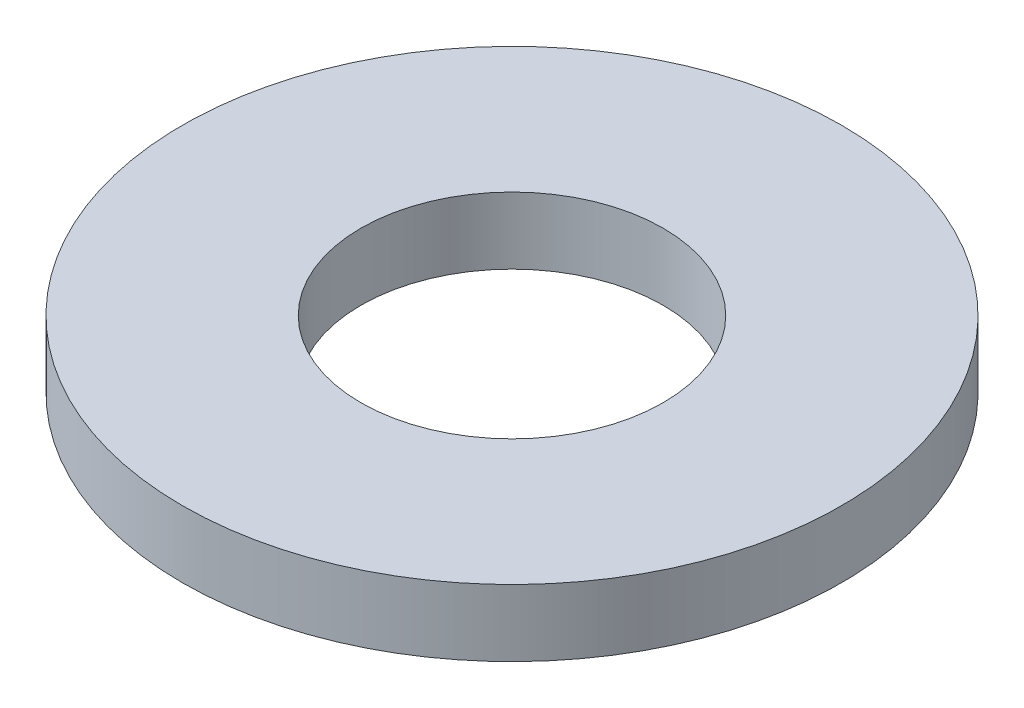
SolidWorks part; units mm, degrees
material "AISI 304"
ref_plane "Front Plane" through (0, 0, 0) normal (0, 0, 1) x (1, 0, 0)
ref_plane "Top Plane" through (0, 0, 0) normal (0, 1, 0) x (1, 0, 0)
ref_plane "Right Plane" through (0, 0, 0) normal (1, 0, 0) x (0, 0, -1)
sketch "Sketch1" plane through (0, 0, 0) normal (0, 1, 0) x (1, 0, 0)
  circle A0 centre (0, 0) radius 4.7625
  dimension "OD" = 9.525
extrude "Boss-Extrude1" add sketch "Sketch1" along normal blind 0.9652
sketch "Sketch5" plane through (0, 0.9652, 0) normal (0, 1, 0) x (-1, 0, 0)
  circle A0 centre (0, 0) radius 2.1844
  dimension "ID" = 4.3688
extrude "Cut-Extrude1" cut sketch "Sketch5" against normal through all
